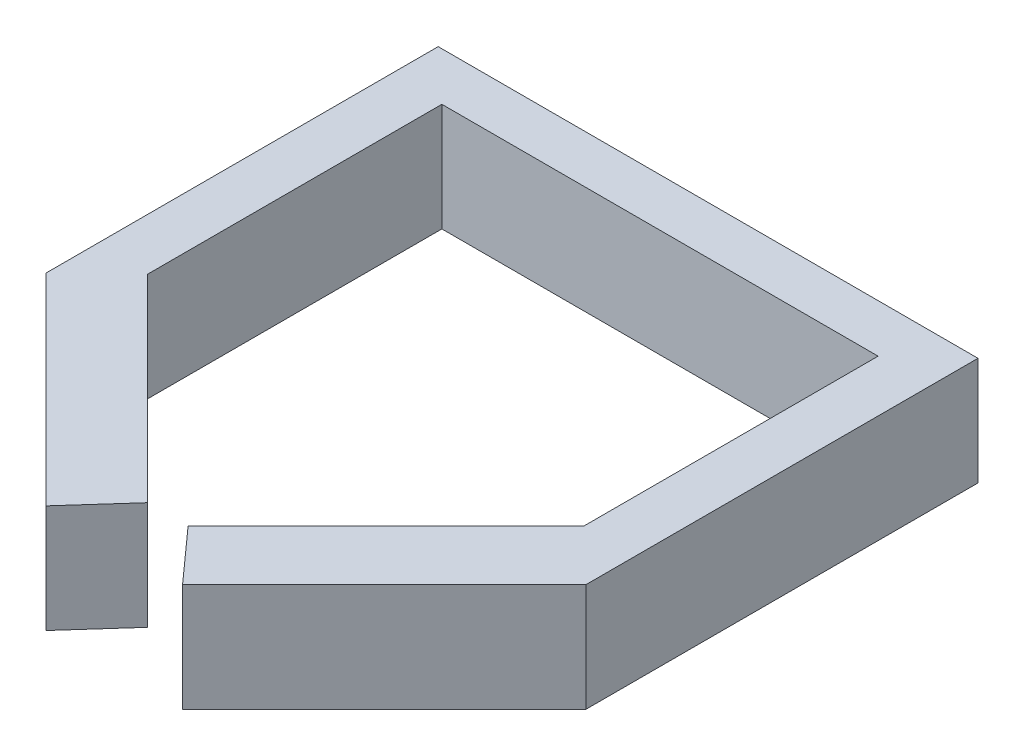
SolidWorks part; units mm, degrees
ref_plane "Front Plane" through (0, 0, 0) normal (0, 0, 1) x (1, 0, 0)
ref_plane "Top Plane" through (0, 0, 0) normal (0, 1, 0) x (1, 0, 0)
ref_plane "Right Plane" through (0, 0, 0) normal (1, 0, 0) x (0, 0, -1)
sketch "Sketch1" plane through (0, 0, 0) normal (0, 1, 0) x (1, 0, 0)
  line L0 (0, 18.676) -> (18.676, 0)
  line L2 (0, 18.676) -> (0, 55)
  line L3 (0, 55) -> (50, 55)
  line L4 (50, 18.676) -> (50, 55)
  line L6 (50, 18.676) -> (31.324, 0)
  line L7 (45.2025, 50.5452) -> (4.7975, 50.5452)
  line L8 (4.7975, 50.5452) -> (4.7975, 23.3022)
  line L9 (4.7975, 23.3022) -> (23.1308, 4.9688)
  line L10 (45.2025, 23.3022) -> (26.8692, 4.9688)
  line L11 (45.2025, 50.5452) -> (45.2025, 23.3022)
  line L12 (18.676, 0) -> (23.1308, 4.9688)
  line L13 (31.324, 0) -> (26.8692, 4.9688)
  point P14 (25, 50.5452)
extrude "Boss-Extrude1" add sketch "Sketch1" along normal blind 10
